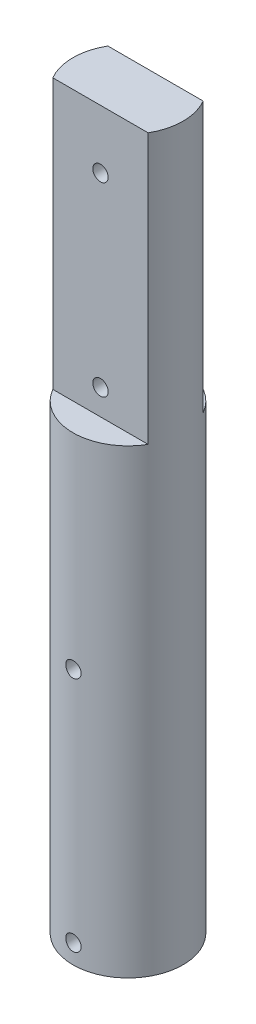
SolidWorks part; units mm, degrees
ref_plane "Front Plane" through (0, 0, 0) normal (0, 0, 1) x (1, 0, 0)
ref_plane "Top Plane" through (0, 0, 0) normal (0, 1, 0) x (1, 0, 0)
ref_plane "Right Plane" through (0, 0, 0) normal (1, 0, 0) x (0, 0, -1)
sketch "Sketch1" plane through (0, 0, 0) normal (0, 1, 0) x (1, 0, 0)
  line L0 (-4.3, 4.3) -> (4.3, 4.3)
  line L1 (-4.5, -4.5) -> (4.5, -4.5) construction
  line L2 (-4.5, -4.5) -> (-4.5, 4.5) construction
  line L3 (-4.5, 4.5) -> (4.5, 4.5) construction
  line L4 (4.5, -4.5) -> (4.5, 4.5) construction
  line L5 (4.3, -4.3) -> (4.3, 4.3)
  line L6 (-4.3, -4.3) -> (4.3, -4.3)
  line L7 (-4.3, -4.3) -> (-4.3, 4.3)
  point P0 (0, 0)
  dimension "D1" = 9
  dimension "D2" = 9
  dimension "D3" = 0.2
sketch "Sketch2" plane through (0, 0, 0) normal (0, 1, 0) x (1, 0, 0)
  circle A0 centre (0, 0) radius 4.3
extrude "Boss-Extrude2" add sketch "Sketch2" along normal blind 57.08
sketch "Sketch4" plane through (0, 57.08, 0) normal (0, 1, 0) x (1, 0, 0)
  line L0 (0, 4.3) -> (0, 0) construction
  line L1 (-4.3, 0) -> (4.3, 0) construction
  line L2 (0, 2.15) -> (-3.7239, 2.15)
  line L3 (0, 2.15) -> (3.7239, 2.15)
  line L4 (0, -2.15) -> (-3.7239, -2.15)
  line L5 (0, -2.15) -> (3.7239, -2.15)
  circle A1 centre (0, 0) radius 4.3 construction
  arc A2 (-3.7239, 2.15) -> (3.7239, 2.15) centre (0, 0) cw
  arc A3 (-3.7239, -2.15) -> (3.7239, -2.15) centre (0, 0) ccw
extrude "Cut-Extrude2" cut sketch "Sketch4" against normal blind 21.08
sketch "Sketch5" plane through (0, 57.08, 0) normal (0, 1, 0) x (1, 0, 0)
  line L2 (-3.7239, -2.15) -> (3.7239, -2.15)
  line L3 (3.7239, 2.15) -> (-3.7239, 2.15)
  line L4 (-3.7239, -2.15) -> (3.7239, -2.15)
  line L5 (3.7239, 2.15) -> (-3.7239, 2.15)
  arc A2 (3.7239, -2.15) -> (3.7239, 2.15) centre (0, 0) ccw
  arc A3 (-3.7239, 2.15) -> (-3.7239, -2.15) centre (0, 0) ccw
  arc A4 (3.7239, -2.15) -> (3.7239, 2.15) centre (0, 0) ccw
  arc A5 (-3.7239, 2.15) -> (-3.7239, -2.15) centre (0, 0) ccw
  dimension "D1" = 0
sketch "Sketch6" plane through (0, 0, 0) normal (0, 0, 1) x (1, 0, 0)
  line L0 (0, 0) -> (0, 3) construction
  circle A0 centre (0, 1.5) radius 0.6
extrude "Cut-Extrude3" cut sketch "Sketch6" against normal through all both and the other way through all
sketch "Sketch7" plane through (0, 0, 2.15) normal (0, 0, 1) x (1, 0, 0)
  line L0 (0, 36) -> (0, 38) construction
  line L1 (3.7239, 36) -> (-3.7239, 36) construction
  circle A0 centre (0, 38) radius 0.6
  dimension "D1" = 2
extrude "Cut-Extrude4" cut sketch "Sketch7" against normal blind 10
sketch "Sketch8" plane through (0, 0, 0) normal (0, 0, 1) x (1, 0, 0)
  line L0 (0, 38) -> (0, 20) construction
  circle A0 centre (0, 20) radius 0.6
  dimension "D1" = 18
extrude "Cut-Extrude5" cut sketch "Sketch8" against normal through all both and the other way through all
sketch "Sketch9" plane through (0, 0, 2.15) normal (0, 0, 1) x (1, 0, 0)
  line L0 (0, 38) -> (0, 52.5) construction
  line L1 (-3.7239, 46.54) -> (3.7239, 46.54) construction
  line L2 (-3.7239, 36) -> (-3.7239, 57.08) construction
  line L3 (3.7239, 36) -> (3.7239, 57.08) construction
  circle A0 centre (0, 52.5) radius 0.6
  dimension "D1" = 14.5
extrude "Cut-Extrude6" cut sketch "Sketch9" against normal through all
